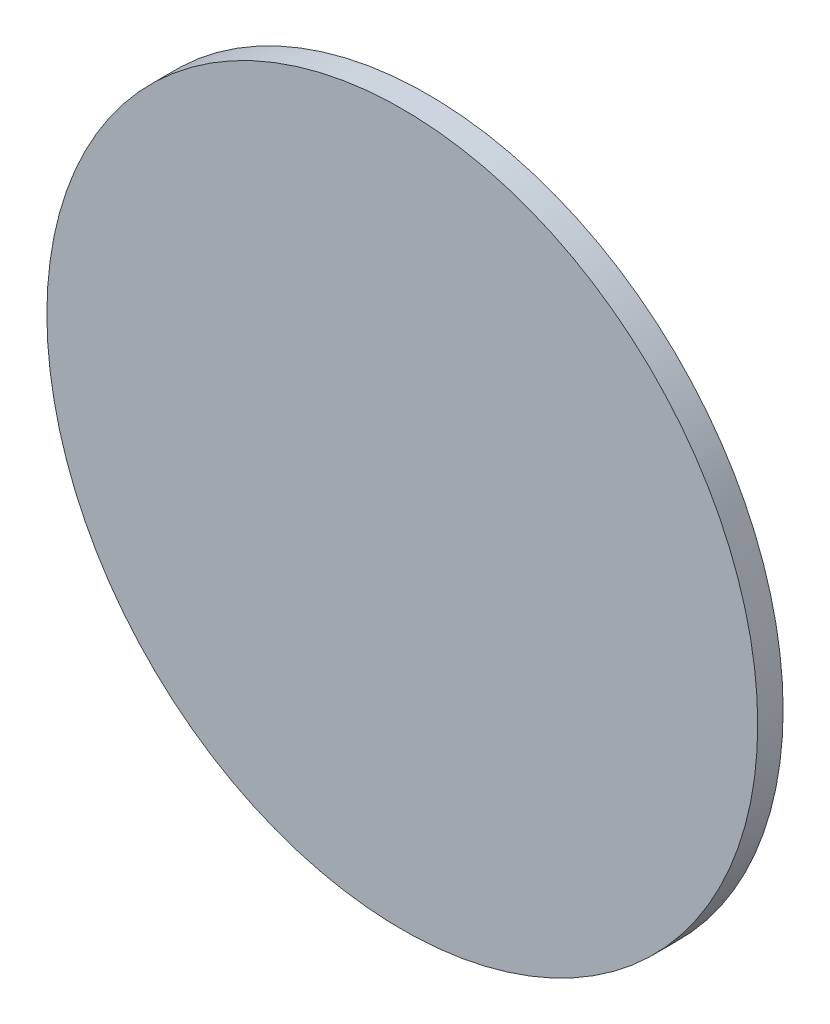
SolidWorks part; units mm, degrees
ref_plane "Front" through (0, 0, 0) normal (0, 0, 1) x (1, 0, 0)
ref_plane "Top" through (0, 0, 0) normal (0, 1, 0) x (1, 0, 0)
ref_plane "Right" through (0, 0, 0) normal (1, 0, 0) x (0, 0, -1)
sketch "Sketch1" plane through (0, 0, 0) normal (0, 0, 1) x (1, 0, 0)
  circle A0 centre (0, 0) radius 44.45
  dimension "D1" = 88.9
extrude "Extrude1" add sketch "Sketch1" along normal blind 3.175
